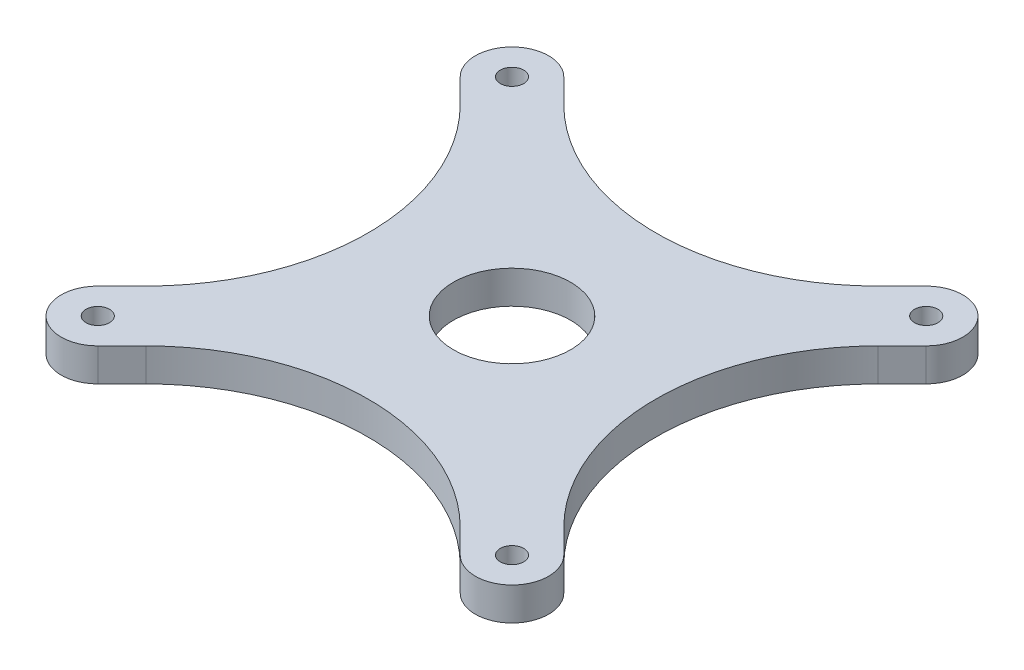
SolidWorks part; units mm, degrees
material "6061 合金"
ref_plane "前视基准面" through (0, 0, 0) normal (0, 0, 1) x (1, 0, 0)
ref_plane "上视基准面" through (0, 0, 0) normal (0, 1, 0) x (1, 0, 0)
ref_plane "右视基准面" through (0, 0, 0) normal (1, 0, 0) x (0, 0, -1)
sketch "草图1" plane through (0, 0, 0) normal (0, 1, 0) x (1, 0, 0)
  line L1 (-35, -35) -> (35, -35)
  line L2 (-35, -35) -> (-35, 35)
  line L3 (-35, 35) -> (35, 35)
  line L4 (35, -35) -> (35, 35)
  line L5 (-35, -35) -> (35, 35) construction
  line L6 (-35, 35) -> (35, -35) construction
  point P0 (0, 0)
  dimension "D1" = 70
  dimension "D2" = 70
extrude "凸台-拉伸1" add sketch "草图1" along normal blind 5
sketch "草图2" plane through (0, 5, 0) normal (0, 1, 0) x (1, 0, 0)
  circle A0 centre (0, 0) radius 8
  dimension "D1" = 16
extrude "切除-拉伸1" cut sketch "草图2" against normal blind 2.5
sketch "草图3" plane through (0, 2.5, 0) normal (0, 1, 0) x (1, 0, 0)
  circle A0 centre (0, 0) radius 6.5
  dimension "D1" = 13
extrude "切除-拉伸2" cut sketch "草图3" against normal up to next
sketch "草图4" plane through (0, 0, 0) normal (0, -1, 0) x (1, 0, 0)
  line L1 (35, 35) -> (-35, 35)
  line L2 (35, 35) -> (35, -35)
  line L3 (35, -35) -> (-35, -35)
  line L4 (-35, 35) -> (-35, -35)
  line L5 (35, 35) -> (-35, -35) construction
  line L6 (35, -35) -> (-35, 35) construction
  circle A0 centre (0, 0) radius 10
  dimension "D1" = 20
  dimension "D2" = 70
  dimension "D3" = 70
extrude "切除-拉伸3" cut sketch "草图4" against normal blind 0.5
sketch "草图5" plane through (0, 5, 0) normal (0, 1, 0) x (1, 0, 0)
  line L0 (0, 0) -> (35, -35) construction
  circle A0 centre (28.2843, -28.2843) radius 1.6
  circle A1 centre (-28.2843, -28.2843) radius 1.6
  circle A2 centre (-28.2843, 28.2843) radius 1.6
  circle A3 centre (28.2843, 28.2843) radius 1.6
  point P4 (28.2843, -28.2843)
  point P16 (0, 0)
  dimension "D2" = 3.2
  dimension "D1" = 40
  dimension "D3" = 4
extrude "切除-拉伸4" cut sketch "草图5" against normal up to next
sketch "草图6" plane through (0, 0.5, 0) normal (0, -1, 0) x (1, 0, 0)
  line L0 (0, 12.5) -> (0, 35) construction
  line L1 (35, 35) -> (-35, 35) construction
  line L2 (35, 35) -> (0, 0) construction
  line L3 (27.9289, 35) -> (4.5654, 11.6365)
  line L4 (-27.9289, 35) -> (-4.5654, 11.6365)
  line L5 (31.4645, 38.5355) -> (-3.5355, 3.5355) construction
  line L6 (27.9289, 35) -> (-27.9289, 35)
  line L7 (35, -27.9289) -> (11.6365, -4.5654)
  line L8 (35, 27.9289) -> (11.6365, 4.5654)
  line L9 (35, -27.9289) -> (35, 27.9289)
  line L10 (-27.9289, -35) -> (-4.5654, -11.6365)
  line L11 (27.9289, -35) -> (4.5654, -11.6365)
  line L12 (-27.9289, -35) -> (27.9289, -35)
  line L13 (-35, 27.9289) -> (-11.6365, 4.5654)
  line L14 (-35, -27.9289) -> (-11.6365, -4.5654)
  line L15 (-35, 27.9289) -> (-35, -27.9289)
  arc A0 (4.5654, 11.6365) -> (-4.5654, 11.6365) centre (0, 0) ccw
  arc A1 (11.6365, -4.5654) -> (11.6365, 4.5654) centre (0, 0) ccw
  arc A2 (-4.5654, -11.6365) -> (4.5654, -11.6365) centre (0, 0) ccw
  arc A3 (-11.6365, 4.5654) -> (-11.6365, -4.5654) centre (0, 0) ccw
  point P29 (0, 0)
  point P30 (0, 0)
  dimension "D1" = 25
  dimension "D2" = 5
  dimension "D3" = 4
extrude "切除-拉伸6" cut sketch "草图6" against normal up to next
sketch "草图7" plane through (0, 0.5, 0) normal (0, -1, 0) x (1, 0, 0)
  line L0 (35, 27.9289) -> (35, 35) construction
  line L1 (35, 35) -> (27.9289, 35) construction
  line L2 (4.5654, 11.6365) -> (27.9289, 35) construction
  line L3 (35, 27.9289) -> (11.6365, 4.5654) construction
  line L4 (35, 27.9289) -> (35, 35)
  line L5 (35, 35) -> (27.9289, 35)
  line L6 (24.7487, 31.8198) -> (27.9289, 35)
  line L7 (35, 27.9289) -> (31.8198, 24.7487)
  line L8 (27.9289, -35) -> (24.7487, -31.8198)
  line L9 (31.8198, -24.7487) -> (35, -27.9289)
  line L10 (35, -35) -> (35, -27.9289)
  line L11 (27.9289, -35) -> (35, -35)
  line L12 (-35, -27.9289) -> (-31.8198, -24.7487)
  line L13 (-24.7487, -31.8198) -> (-27.9289, -35)
  line L14 (-35, -35) -> (-27.9289, -35)
  line L15 (-35, -27.9289) -> (-35, -35)
  line L16 (-27.9289, 35) -> (-24.7487, 31.8198)
  line L17 (-31.8198, 24.7487) -> (-35, 27.9289)
  line L18 (-35, 35) -> (-35, 27.9289)
  line L19 (-27.9289, 35) -> (-35, 35)
  arc A0 (31.8198, 24.7487) -> (24.7487, 31.8198) centre (28.2843, 28.2843) ccw
  arc A1 (24.7487, -31.8198) -> (31.8198, -24.7487) centre (28.2843, -28.2843) ccw
  arc A2 (-31.8198, -24.7487) -> (-24.7487, -31.8198) centre (-28.2843, -28.2843) ccw
  arc A3 (-24.7487, 31.8198) -> (-31.8198, 24.7487) centre (-28.2843, 28.2843) ccw
  point P32 (0, 0)
  dimension "D1" = 10
  dimension "D2" = 4
extrude "切除-拉伸7" cut sketch "草图7" against normal up to next
fillet "圆角1" radius 10 8 edges at (11.6365, 2.75, -4.5654) (11.6365, 2.75, 4.5654) (4.5654, 2.75, 11.6365) (-4.5654, 2.75, 11.6365) (-11.6365, 2.75, 4.5654) (-11.6365, 2.75, -4.5654) (-4.5654, 2.75, -11.6365) (4.5654, 2.75, -11.6365)
sketch "草图8" plane through (0, 0, 0) normal (0, -1, 0) x (1, 0, 0)
  circle A0 centre (0, 0) radius 10
  dimension "D1" = 20
extrude "切除-拉伸8" cut sketch "草图8" against normal blind 0.5
sketch "草图9" plane through (0, 0.5, 0) normal (0, -1, 0) x (1, 0, 0)
  line L0 (0, 0) -> (0, 53.0164) construction
  line L1 (-24.7487, 31.8198) -> (-8.323, 15.3941) construction
  line L2 (8.323, 15.3941) -> (24.7487, 31.8198) construction
  line L3 (8.323, 15.3941) -> (21.4645, 28.5355)
  line L4 (-21.4645, 28.5355) -> (-8.323, 15.3941)
  line L5 (28.5355, 21.4645) -> (15.3941, 8.323)
  line L6 (15.3941, -8.323) -> (28.5355, -21.4645)
  line L7 (21.4645, -28.5355) -> (8.323, -15.3941)
  line L8 (-8.323, -15.3941) -> (-21.4645, -28.5355)
  line L9 (-28.5355, -21.4645) -> (-15.3941, -8.323)
  line L10 (-15.3941, 8.323) -> (-28.5355, 21.4645)
  arc A0 (-21.4645, 28.5355) -> (21.4645, 28.5355) centre (0, 50) ccw
  arc A1 (0.6955, 12.4806) -> (8.323, 15.3941) centre (1.2519, 22.4651) ccw construction
  arc A2 (0.6955, 12.4806) -> (-0.6955, 12.4806) centre (0, 0) ccw construction
  arc A3 (-8.323, 15.3941) -> (-0.6955, 12.4806) centre (-1.2519, 22.4651) ccw construction
  arc A4 (0.6955, 12.4806) -> (8.323, 15.3941) centre (1.2519, 22.4651) ccw
  arc A5 (0.6955, 12.4806) -> (-0.6955, 12.4806) centre (0, 0) ccw
  arc A6 (-8.323, 15.3941) -> (-0.6955, 12.4806) centre (-1.2519, 22.4651) ccw
  arc A7 (28.5355, 21.4645) -> (28.5355, -21.4645) centre (50, 0) ccw
  arc A8 (15.3941, 8.323) -> (12.4806, 0.6955) centre (22.4651, 1.2519) ccw
  arc A9 (12.4806, -0.6955) -> (12.4806, 0.6955) centre (0, 0) ccw
  arc A10 (12.4806, -0.6955) -> (15.3941, -8.323) centre (22.4651, -1.2519) ccw
  arc A11 (21.4645, -28.5355) -> (-21.4645, -28.5355) centre (0, -50) ccw
  arc A12 (8.323, -15.3941) -> (0.6955, -12.4806) centre (1.2519, -22.4651) ccw
  arc A13 (-0.6955, -12.4806) -> (0.6955, -12.4806) centre (0, 0) ccw
  arc A14 (-0.6955, -12.4806) -> (-8.323, -15.3941) centre (-1.2519, -22.4651) ccw
  arc A15 (-28.5355, -21.4645) -> (-28.5355, 21.4645) centre (-50, 0) ccw
  arc A16 (-15.3941, -8.323) -> (-12.4806, -0.6955) centre (-22.4651, -1.2519) ccw
  arc A17 (-12.4806, 0.6955) -> (-12.4806, -0.6955) centre (0, 0) ccw
  arc A18 (-12.4806, 0.6955) -> (-15.3941, 8.323) centre (-22.4651, 1.2519) ccw
  point P44 (0, 0)
  dimension "D1" = 50
  dimension "D2" = 4
extrude "凸台-拉伸2" add sketch "草图9" against normal up to surface (4.5 mm away) up to face at (28.2843, 5, -26.6843)
sketch "草图10" plane through (0, 2.5, 0) normal (0, 1, 0) x (1, 0, 0)
  circle A0 centre (0, 0) radius 6.5 construction
  circle A1 centre (0, 0) radius 8
  circle A2 centre (0, 0) radius 8
  circle A3 centre (0, 0) radius 6.5
  dimension "D1" = 0
extrude "切除-拉伸9" cut sketch "草图10" against normal up to next
